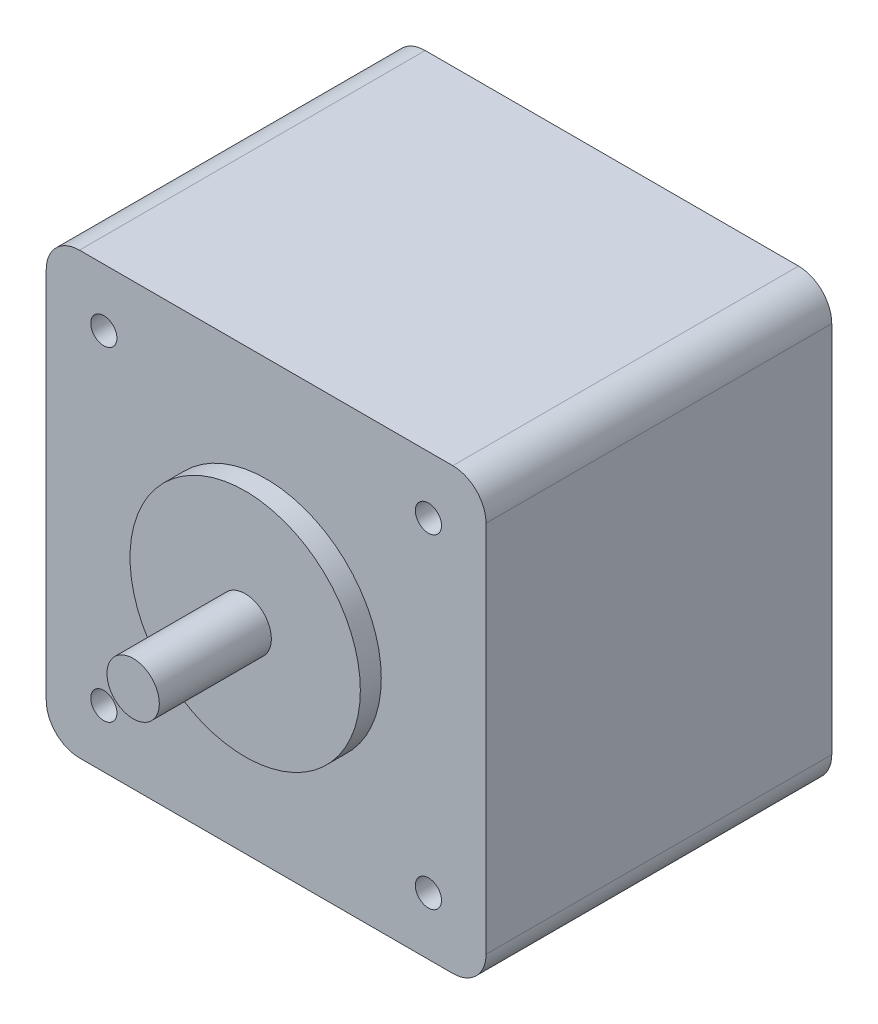
SolidWorks part; units mm, degrees
ref_plane "Front Plane" through (0, 0, 0) normal (0, 0, 1) x (1, 0, 0)
ref_plane "Top Plane" through (0, 0, 0) normal (0, 1, 0) x (1, 0, 0)
ref_plane "Right Plane" through (0, 0, 0) normal (1, 0, 0) x (0, 0, -1)
ref_plane "Plane1" through (0, 0, 33.02) normal (0, 0, 1) x (1, 0, 0)
sketch "Sketch1" plane through (0, 0, 33.02) normal (0, 0, 1) x (1, 0, 0)
  line L0 (21, -21) -> (21, 21)
  line L1 (21, 21) -> (-21, 21)
  line L2 (-21, 21) -> (-21, -21)
  line L3 (-21, -21) -> (21, -21)
  dimension "D1" = 42
  dimension "D2" = 42
  dimension "D3" = 21
  dimension "D4" = 21
extrude "Boss-Extrude1" add sketch "Sketch1" against normal blind 33.02
ref_plane "Plane2" through (0, 0, 2.2098) normal (0, 0, -1) x (-1, 0, 0)
sketch "Sketch6" plane through (0, 0, 0) normal (0, 1, 0) x (1, 0, 0)
  line L0 (10.9982, -33.02) -> (0, -33.02)
  line L1 (0, -33.02) -> (0, -45.72)
  line L2 (0, -45.72) -> (2.5, -45.72)
  line L3 (2.5, -45.72) -> (2.5, -35.02)
  line L4 (2.5, -35.02) -> (10.9982, -35.02)
  line L5 (10.9982, -35.02) -> (10.9982, -33.02)
  line L6 (0, -33.02) -> (0, -45.72) construction
  line L7 (-55, -33.02) -> (55, -33.02) construction
  line L8 (21, 0) -> (21, -33.02) construction
  dimension "D1" = 12.7
  dimension "D2" = 2
  dimension "D3" = 10.9982
  dimension "D4" = 33.02
  dimension "D5" = 21
  dimension "D6" = 2.5
revolve "Revolve5" add sketch "Sketch6" angle 360 about L6
hole_wizard "M3x0.5 Tapped Hole1" positions "Sketch8" profile "Sketch7" tap size "M3x0.5" standard "Ansi Metric"
sketch "Sketch8" plane through (0, 0, 33.02) normal (0, 0, 1) x (1, 0, 0)
  point P3 (-15.5, 15.5)
  point P13 (-15.5, -15.5)
  point P14 (15.5, -15.5)
  point P15 (15.5, 15.5)
  dimension "D1" = 15.5
  dimension "D2" = 15.5
sketch "Sketch7" plane through (-15.5, 15.5, 33.02) normal (1, 0, 0) x (0, -1, 0)
  line L0 (0, 0) -> (0, 8.2511)
  line L1 (0, 8.2511) -> (1.25, 7.5)
  line L2 (1.25, 7.5) -> (1.25, 0)
  line L5 (1.25, 0) -> (0, 0)
  line L10 (0, 8.2511) -> (-1.25, 7.5) construction
  line L11 (0, -6.35) -> (0, 107.95) construction
  dimension "Tap Drill Dia." = 2.5
  dimension "Tap Drill Depth" = 7.5
  dimension "Drill Angle" = 118
fillet "Fillet1" radius 3.175 4 edges at (-21, 21, 16.51) (21, 21, 16.51) (-21, -21, 16.51) (21, -21, 16.51)
